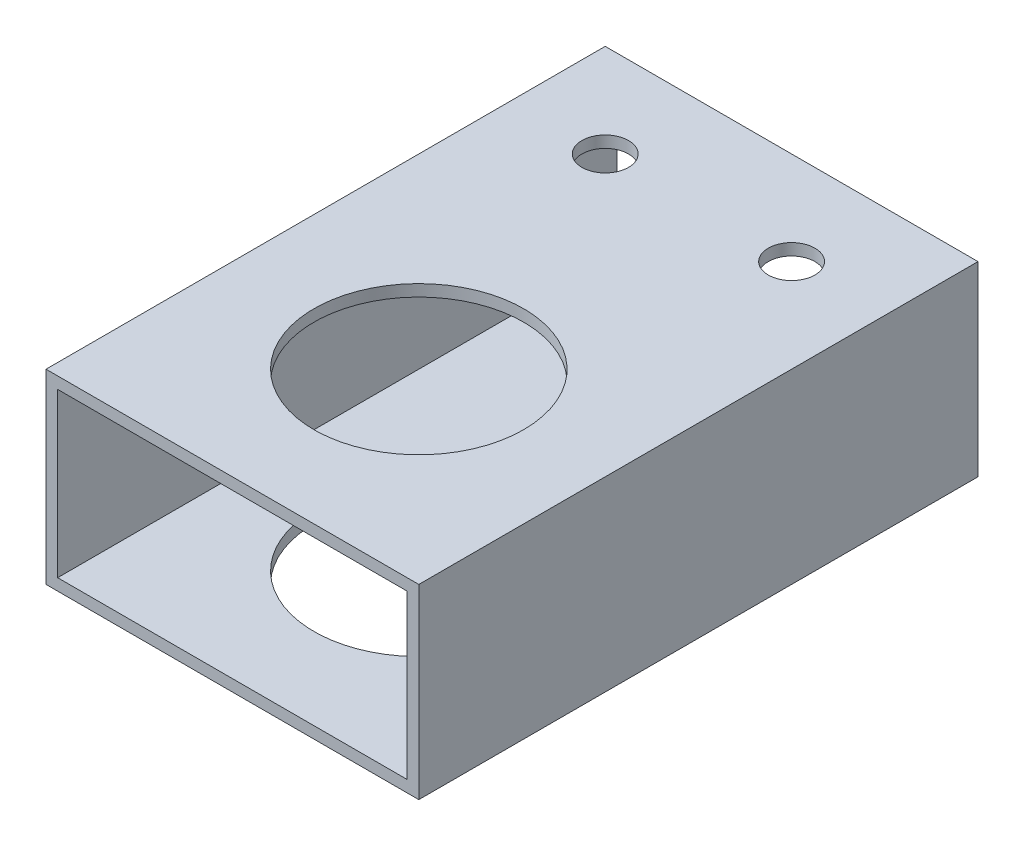
SolidWorks part; units mm, degrees
ref_plane "Front Plane" through (0, 0, 0) normal (0, 0, 1) x (1, 0, 0)
ref_plane "Top Plane" through (0, 0, 0) normal (0, 1, 0) x (1, 0, 0)
ref_plane "Right Plane" through (0, 0, 0) normal (1, 0, 0) x (0, 0, -1)
sketch "Sketch1" plane through (0, 0, 0) normal (0, 0, 1) x (1, 0, 0)
  line L1 (23.8125, -11.1125) -> (-23.8125, -11.1125)
  line L2 (23.8125, -11.1125) -> (23.8125, 11.1125)
  line L3 (23.8125, 11.1125) -> (-23.8125, 11.1125)
  line L4 (-23.8125, -11.1125) -> (-23.8125, 11.1125)
  line L5 (23.8125, -11.1125) -> (-23.8125, 11.1125) construction
  line L6 (23.8125, 11.1125) -> (-23.8125, -11.1125) construction
  line L7 (25.4, -12.7) -> (-25.4, -12.7)
  line L8 (25.4, -12.7) -> (25.4, 12.7)
  line L9 (25.4, 12.7) -> (-25.4, 12.7)
  line L10 (-25.4, -12.7) -> (-25.4, 12.7)
  line L11 (25.4, -12.7) -> (-25.4, 12.7) construction
  line L12 (25.4, 12.7) -> (-25.4, -12.7) construction
  point P0 (0, 0)
  point P6 (0, 0)
  dimension "D1" = 50.8
  dimension "D2" = 25.4
  dimension "D3" = 1.5875
  dimension "D4" = 1.5875
extrude "Boss-Extrude1" add sketch "Sketch1" along normal blind 76.2
sketch "Sketch2" plane through (0, -12.7, 0) normal (0, -1, 0) x (1, 0, 0)
  line L0 (0, 0) -> (0, 50.8) construction
  line L1 (-25.4, 0) -> (25.4, 0) construction
  circle A0 centre (0, 50.8) radius 14.2875
  dimension "D2" = 28.575
  dimension "D1" = 50.8
extrude "Cut-Extrude1" cut sketch "Sketch2" against normal through all
sketch "Sketch3" plane through (0, 12.7, 0) normal (0, 1, 0) x (1, 0, 0)
  line L0 (0, 0) -> (0, -12.7) construction
  line L1 (0, -12.7) -> (12.7, -12.7) construction
  line L2 (-12.7, -12.7) -> (0, -12.7) construction
  line L4 (12.7, 12.7) -> (0, 12.7) construction
  line L5 (0, 12.7) -> (-12.7, 12.7) construction
  line L6 (25.4, 0) -> (63.5, 0) construction
  line L7 (63.5, 0) -> (63.5, 50.8) construction
  line L8 (63.5, 50.8) -> (-63.5, 50.8) construction
  line L9 (-63.5, 50.8) -> (-63.5, 0) construction
  line L10 (-63.5, 0) -> (-25.4, 0) construction
  line L11 (12.7, 38.1) -> (12.7, 12.7) construction
  line L12 (-12.7, 12.7) -> (-12.7, 38.1) construction
  circle A0 centre (12.7, -12.7) radius 3.175
  circle A1 centre (-12.7, -12.7) radius 3.175
  circle A2 centre (-12.7, 12.7) radius 3.175
  circle A3 centre (12.7, 12.7) radius 3.175
  circle A5 centre (12.7, 38.1) radius 3.175
  circle A6 centre (-12.7, 38.1) radius 3.175
  dimension "D3" = 6.35
  dimension "D7" = 12.7
  dimension "D1" = 12.7
  dimension "D2" = 25.4
  dimension "D4" = 50.8
  dimension "D5" = 127
  dimension "D6" = 25.4
extrude "Cut-Extrude2" cut sketch "Sketch3" against normal blind 25.4
